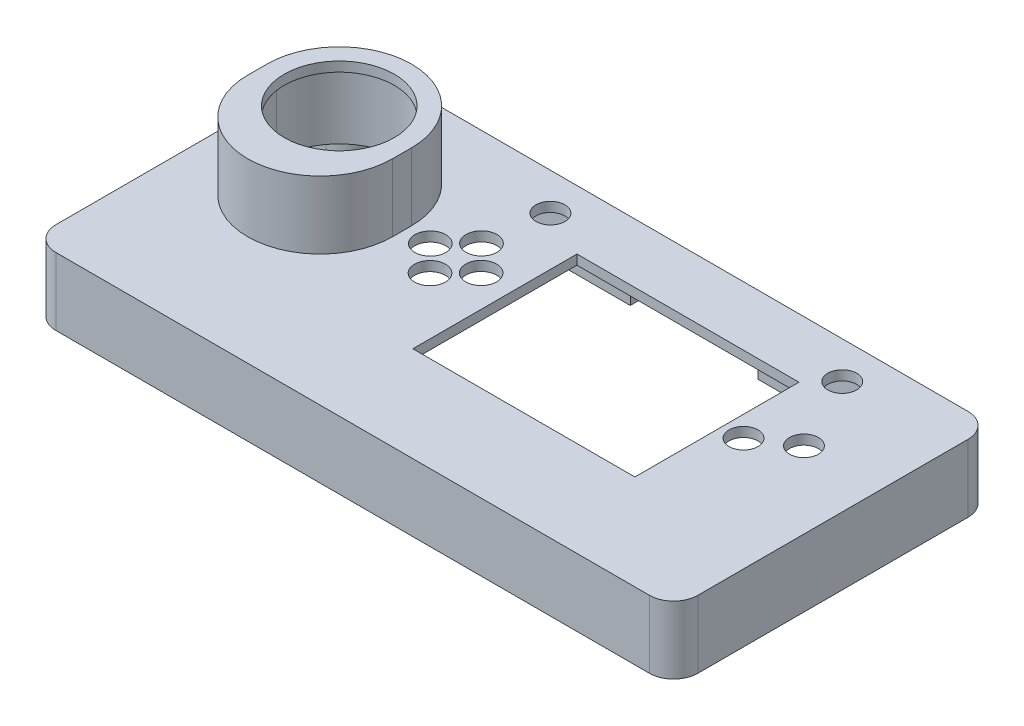
SolidWorks part; units mm, degrees
ref_plane "정면" through (0, 0, 0) normal (0, 0, 1) x (1, 0, 0)
ref_plane "윗면" through (0, 0, 0) normal (0, 1, 0) x (1, 0, 0)
ref_plane "우측면" through (0, 0, 0) normal (1, 0, 0) x (0, 0, -1)
sketch "스케치1" plane through (0, 0, 0) normal (0, 1, 0) x (1, 0, 0)
  line L0 (-61.4984, 66.0105) -> (61.5016, 65.9895)
  line L1 (66.5008, 60.9895) -> (66.5008, 4.9895)
  line L2 (61.5, -0.0105) -> (-61.5, 0.0105)
  line L3 (-66.4992, 5.0105) -> (-66.4992, 61.0105)
  line L4 (-7.2562, 53.7133) -> (38.7438, 53.7133)
  line L5 (38.7438, 53.7133) -> (38.7438, 19.7133)
  line L6 (38.7438, 19.7133) -> (-7.2562, 19.7133)
  line L7 (-7.2562, 19.7133) -> (-7.2562, 53.7133)
  arc A0 (66.5008, 60.9895) -> (61.5016, 65.9895) centre (61.5008, 60.9895) ccw
  arc A1 (61.5, -0.0105) -> (66.5008, 4.9895) centre (61.5008, 4.9895) ccw
  arc A2 (-66.4992, 5.0105) -> (-61.5, 0.0105) centre (-61.4992, 5.0105) ccw
  arc A3 (-61.4984, 66.0105) -> (-66.4992, 61.0105) centre (-61.4992, 61.0105) ccw
  circle A4 centre (-19.0542, 45.7303) radius 3.2
  circle A5 centre (-24.3247, 40.3963) radius 3.2
  circle A6 centre (-13.7837, 40.3963) radius 3.2
  circle A7 centre (-19.0542, 35.0623) radius 3.2
  circle A8 centre (-17.3397, 58.3033) radius 3
  circle A9 centre (43.1123, 58.3033) radius 3
  circle A10 centre (50.6758, 42.8113) radius 3
  circle A11 centre (43.0488, 37.9198) radius 3
extrude "보스-돌출1" add sketch "스케치1" along normal blind 13
sketch "스케치2" plane through (0, 13, 0) normal (0, 1, 0) x (1, 0, 0)
  line L0 (124.3082, -0.0113) -> (137.3082, -0.0113)
  line L1 (-29.4542, 41.6663) -> (-29.4542, 37.697)
  line L2 (-59.4542, 41.6663) -> (-59.4542, 37.697)
  circle A0 centre (-44.4542, 41.6663) radius 11.4
  arc A1 (-29.4542, 41.6663) -> (-59.4542, 41.6663) centre (-44.4542, 41.6663) ccw
  arc A2 (-59.4542, 37.697) -> (-44.4542, 22.697) centre (-44.4542, 37.697) ccw
  arc A3 (-44.4542, 22.697) -> (-29.4542, 37.697) centre (-44.4542, 37.697) ccw
extrude "보스-돌출2" add sketch "스케치2" along normal blind 14 contours A2 A3 L1 A1 L2 A0
sketch "스케치3" plane through (0, 0, 0) normal (0, -1, 0) x (1, 0, 0)
  line L14 (-56.5008, -64.0096) -> (56.5008, -63.9904)
  line L15 (64.5008, -55.9895) -> (64.5008, -9.9895)
  line L16 (56.5008, -1.9904) -> (-56.5008, -2.0096)
  line L17 (-64.4992, -9.9895) -> (-64.4992, -55.9895)
  line L20 (56.5008, -60.9895) -> (56.5008, -63.9904)
  line L21 (61.5008, -55.9895) -> (64.5008, -55.9895)
  line L22 (56.5008, -4.9895) -> (56.5008, -1.9904)
  line L23 (61.5008, -9.9895) -> (64.5008, -9.9895)
  line L24 (-56.5008, -60.9895) -> (-56.5008, -64.0096)
  line L25 (-61.5008, -55.9895) -> (-64.4992, -55.9895)
  line L26 (-56.5008, -4.9895) -> (-56.5008, -2.0096)
  line L27 (-61.5008, -9.9895) -> (-64.4992, -9.9895)
  arc A27 (56.5008, -4.9895) -> (61.5008, -9.9895) centre (61.5008, -4.9895) ccw
  arc A28 (61.5008, -55.9895) -> (56.5008, -60.9895) centre (61.5008, -60.9895) ccw
  arc A29 (-61.5008, -9.9895) -> (-56.5008, -4.9895) centre (-61.5008, -4.9895) ccw
  arc A30 (-56.5008, -60.9895) -> (-61.5008, -55.9895) centre (-61.5008, -60.9895) ccw
  circle A31 centre (-60.4401, -59.9288) radius 1.25
  circle A32 centre (-60.4401, -6.0921) radius 1.25
  circle A33 centre (60.4427, -59.9288) radius 1.25
  circle A34 centre (60.4427, -6.0921) radius 1.25
  dimension "D1" = 2.5
  dimension "D2" = 2.5
  dimension "D3" = 2.5
  dimension "D4" = 2.5
extrude "컷-돌출1" cut sketch "스케치3" against normal blind 11
sketch "스케치4" plane through (0, 11, 0) normal (0, -1, 0) x (1, 0, 0)
  line L0 (-31.4542, -41.6663) -> (-31.4542, -37.697)
  line L1 (-57.4542, -41.6663) -> (-57.4542, -37.697)
  arc A0 (-57.4542, -41.6663) -> (-31.4542, -41.6663) centre (-44.4542, -41.6663) ccw
  arc A1 (-44.4542, -24.697) -> (-57.4542, -37.697) centre (-44.4542, -37.697) ccw
  arc A2 (-31.4542, -37.697) -> (-44.4542, -24.697) centre (-44.4542, -37.697) ccw
extrude "컷-돌출2" cut sketch "스케치4" against normal blind 14
sketch "스케치5" plane through (0, 11, 0) normal (0, -1, 0) x (1, 0, 0)
  circle A0 centre (-26.0392, -58.1763) radius 4
  circle A1 centre (52.0658, -58.1763) radius 4
  circle A2 centre (-26.0392, -11.8213) radius 4
  circle A3 centre (52.0658, -11.8213) radius 4
extrude "보스-돌출3" add sketch "스케치5" along normal blind 2
sketch "스케치6" plane through (0, 9, 0) normal (0, -1, 0) x (1, 0, 0)
  circle A0 centre (-26.0392, -58.1763) radius 1.5
  circle A1 centre (52.0658, -58.1763) radius 1.5
  circle A2 centre (52.0658, -11.8213) radius 1.5
  circle A3 centre (-26.0392, -11.8213) radius 1.5
extrude "보스-돌출4" add sketch "스케치6" along normal blind 5
sketch "스케치8" plane through (0, 0, 0) normal (0, -1, 0) x (1, 0, 0)
  line L0 (-64.4992, -9.9895) -> (-64.4992, -55.9895) construction
  line L1 (56.5008, -1.9904) -> (-56.5008, -2.0096) construction
  line L2 (-64.4992, -5.0105) -> (-64.4992, -61.0105)
  line L3 (61.5003, -1.9895) -> (-61.4997, -2.0105)
  line L4 (64.5008, -55.9895) -> (64.5008, -9.9895) construction
  line L9 (64.5008, -60.9895) -> (64.5008, -4.9895)
  line L10 (-56.5008, -64.0096) -> (56.5008, -63.9904) construction
  line L11 (-61.4987, -64.0105) -> (61.5013, -63.9895)
  line L12 (61.5016, -65.9895) -> (-61.4984, -66.0105) construction
  line L13 (61.5016, -65.9895) -> (-61.4984, -66.0105)
  line L14 (66.5008, -4.9895) -> (66.5008, -60.9895) construction
  line L15 (66.5008, -4.9895) -> (66.5008, -60.9895)
  line L16 (-61.5, -0.0105) -> (61.5, 0.0105) construction
  line L17 (-61.5, -0.0105) -> (61.5, 0.0105)
  line L18 (-66.4992, -61.0105) -> (-66.4992, -5.0105) construction
  line L19 (-66.4992, -61.0105) -> (-66.4992, -5.0105)
  arc A0 (64.5008, -60.9895) -> (61.5013, -63.9895) centre (61.5008, -60.9895) cw
  arc A1 (-61.4987, -64.0105) -> (-64.4992, -61.0105) centre (-61.4992, -61.0105) cw
  arc A2 (-64.4992, -5.0105) -> (-61.4997, -2.0105) centre (-61.4992, -5.0105) cw
  arc A3 (61.5003, -1.9895) -> (64.5008, -4.9895) centre (61.5008, -4.9895) cw
  arc A4 (61.5016, -65.9895) -> (66.5008, -60.9895) centre (61.5008, -60.9895) ccw construction
  arc A5 (61.5016, -65.9895) -> (66.5008, -60.9895) centre (61.5008, -60.9895) ccw
  arc A6 (66.5008, -4.9895) -> (61.5, 0.0105) centre (61.5008, -4.9895) ccw construction
  arc A7 (66.5008, -4.9895) -> (61.5, 0.0105) centre (61.5008, -4.9895) ccw
  arc A8 (-61.5, -0.0105) -> (-66.4992, -5.0105) centre (-61.4992, -5.0105) ccw construction
  arc A9 (-61.5, -0.0105) -> (-66.4992, -5.0105) centre (-61.4992, -5.0105) ccw
  arc A10 (-66.4992, -61.0105) -> (-61.4984, -66.0105) centre (-61.4992, -61.0105) ccw construction
  arc A11 (-66.4992, -61.0105) -> (-61.4984, -66.0105) centre (-61.4992, -61.0105) ccw
  dimension "D1" = 3
extrude "보스-돌출5" add sketch "스케치8" along normal blind 1
sketch "스케치9" plane through (0, -1, 0) normal (0, -1, 0) x (1, 0, 0)
  line L3 (20.0008, -69.0517) -> (-6.4992, -69.0517)
  line L4 (20.0008, -69.0517) -> (20.0008, -61.8003)
  line L5 (20.0008, -61.8003) -> (-6.4992, -61.8003)
  line L6 (-6.4992, -69.0517) -> (-6.4992, -61.8003)
extrude "컷-돌출4" cut sketch "스케치9" against normal blind 10
